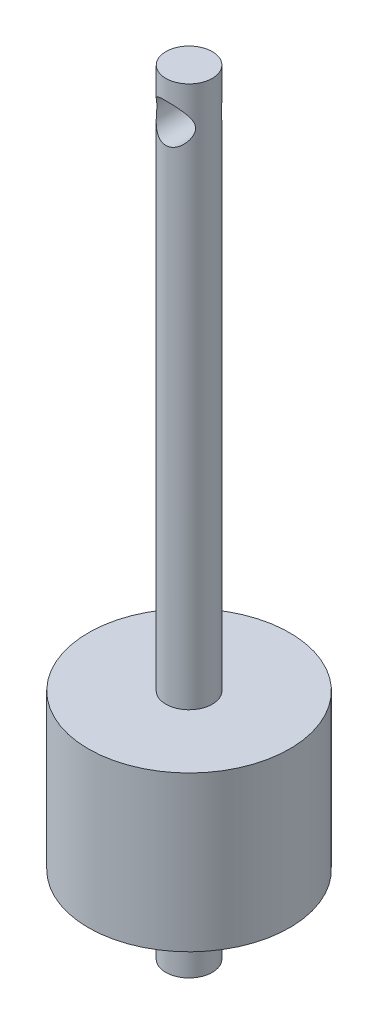
SolidWorks part; units mm, degrees
ref_plane "Plan de face" through (0, 0, 0) normal (0, 0, 1) x (1, 0, 0)
ref_plane "Plan de dessus" through (0, 0, 0) normal (0, 1, 0) x (1, 0, 0)
ref_plane "Plan de droite" through (0, 0, 0) normal (1, 0, 0) x (0, 0, -1)
sketch "Esquisse1" plane through (0, 0, 0) normal (0, 0, 1) x (1, 0, 0)
  line L0 (0, 0) -> (0, -100)
  line L1 (0, -100) -> (-3, -100)
  line L2 (-3, -100) -> (-3, -90)
  line L3 (-3, -90) -> (-13, -90)
  line L4 (-13, -90) -> (-13, -70)
  line L5 (-13, -70) -> (-3, -70)
  line L6 (-3, -70) -> (-3, 0)
  line L7 (-3, 0) -> (0, 0)
  line L8 (-65.6384, -80) -> (60.0945, -80) construction
  dimension "D1" = 100
  dimension "D2" = 20
  dimension "D3" = 80
  dimension "D4" = 3
  dimension "D5" = 10
  dimension "D6" = 3
revolve "Révolution1" add sketch "Esquisse1" angle 360 about L0
sketch "Esquisse2" plane through (0, 0, 0) normal (0, 0, 1) x (1, 0, 0)
  line L0 (3, 0) -> (-3, 0) construction
  line L1 (0, 0) -> (0, -10.1446) construction
  circle A0 centre (0, -5) radius 2.5
  dimension "D2" = 5
  dimension "D1" = 5
extrude "Enlèv. mat.-Extru.1" cut sketch "Esquisse2" against normal through all and the other way through all
